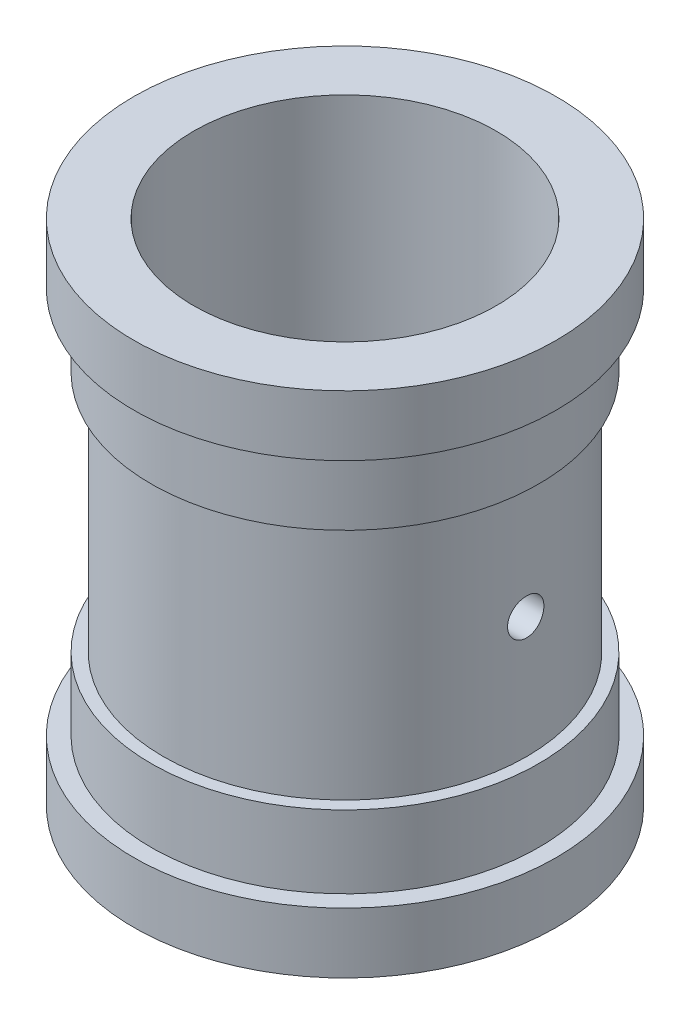
SolidWorks part; units mm, degrees
ref_plane "Front Plane" through (0, 0, 0) normal (0, 0, 1) x (1, 0, 0)
ref_plane "Top Plane" through (0, 0, 0) normal (0, 1, 0) x (1, 0, 0)
ref_plane "Right Plane" through (0, 0, 0) normal (1, 0, 0) x (0, 0, -1)
sketch "Sketch2" plane through (0, 0, 0) normal (0, 0, 1) x (1, 0, 0)
  line L0 (0, 42) -> (0, -42)
  line L1 (0, -42) -> (34.8866, -42)
  line L2 (34.8866, -42) -> (34.8866, -32)
  line L3 (32, -32) -> (34.8866, -32)
  line L4 (32, 32) -> (34.8866, 32)
  line L6 (30, -20) -> (32, -20)
  line L7 (32, -20) -> (32, -32)
  line L8 (30, 20) -> (30, -20)
  line L9 (0, 42) -> (34.8866, 42)
  line L10 (34.8866, 42) -> (34.8866, 32)
  line L12 (32, 20) -> (32, 32)
  line L13 (30, 20) -> (32, 20)
  point P4 (0, 0)
  dimension "D1" = 64
  dimension "D2" = 84
  dimension "D3" = 10
  dimension "D4" = 10
  dimension "D5" = 12
  dimension "D6" = 12
revolve "Revolve2" add sketch "Sketch2" angle 360 about L0
sketch "Sketch4" plane through (0, 42, 0) normal (0, 1, 0) x (1, 0, 0)
  circle A0 centre (0, 0) radius 25
  dimension "D1" = 25
extrude "Cut-Extrude1" cut sketch "Sketch4" against normal blind 106
sketch "Sketch5" plane through (0, 0, 0) normal (1, 0, 0) x (0, 0, -1)
  circle A0 centre (0, 0) radius 3
  dimension "D1" = 3
extrude "Cut-Extrude2" cut sketch "Sketch5" against normal mid plane 70
